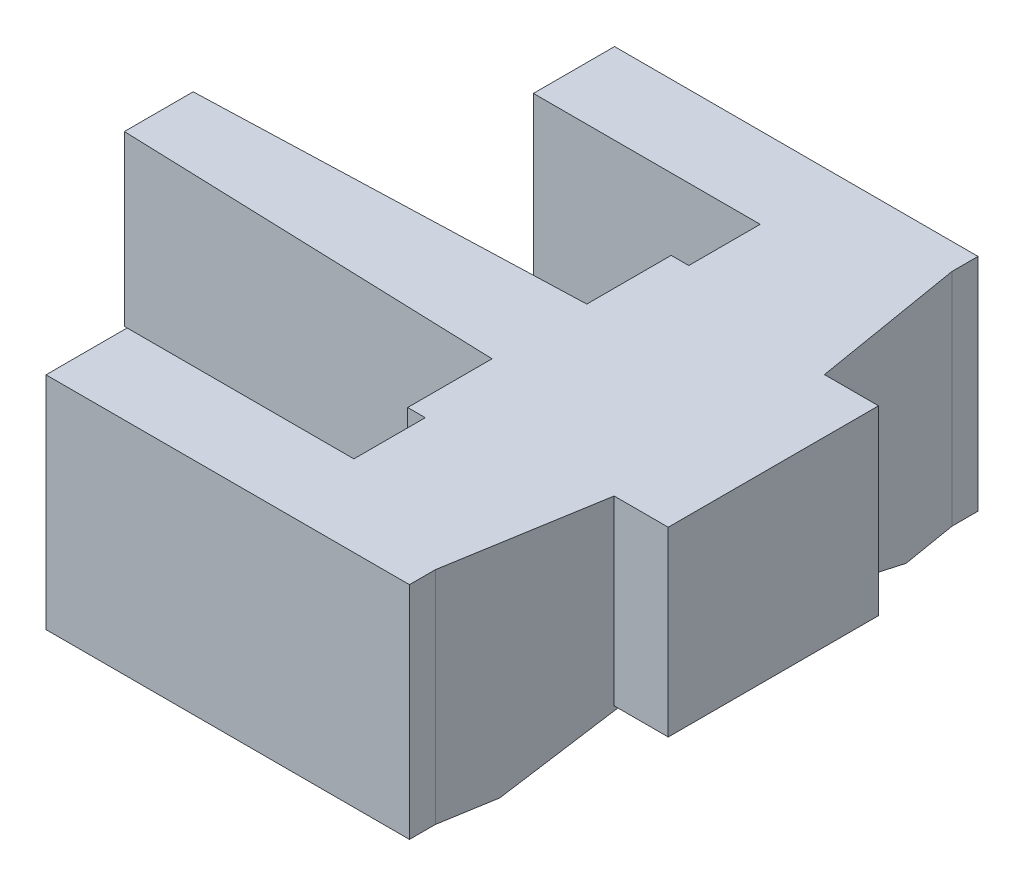
SolidWorks part; units mm, degrees
ref_plane "Front Plane" through (0, 0, 0) normal (0, 0, 1) x (1, 0, 0)
ref_plane "Top Plane" through (0, 0, 0) normal (0, 1, 0) x (1, 0, 0)
ref_plane "Right Plane" through (0, 0, 0) normal (1, 0, 0) x (0, 0, -1)
sketch "Sketch1" plane through (0, 0, 0) normal (0, 1, 0) x (1, 0, 0)
  line L0 (167.303, 457.5748) -> (832.0476, 457.5748) construction
  line L2 (53.2314, 93.5629) -> (55.3687, 80.7629)
  line L3 (55.3687, 80.7629) -> (59.3687, 80.7629)
  line L4 (59.3687, 80.7629) -> (59.3687, 66.5629)
  line L5 (59.3687, 66.5629) -> (55.3687, 66.5629)
  line L6 (55.3687, 66.5629) -> (53.2314, 53.7629)
  line L7 (53.2314, 53.7629) -> (25.2314, 53.7629)
  line L8 (25.2314, 53.7629) -> (25.2314, 58.0129)
  line L9 (25.2314, 58.0129) -> (42.7011, 58.0129)
  line L10 (42.7011, 58.0129) -> (42.7011, 66.5129)
  line L11 (42.7011, 66.5129) -> (41.345, 66.5129)
  line L12 (41.345, 66.5129) -> (41.345, 70.0129)
  line L13 (41.345, 70.0129) -> (12.0187, 71.0129)
  line L14 (12.0187, 71.0129) -> (12.0187, 76.3129)
  line L15 (12.0187, 76.3129) -> (41.345, 77.3129)
  line L16 (41.345, 77.3129) -> (41.345, 80.8129)
  line L17 (41.345, 80.8129) -> (42.7011, 80.8129)
  line L18 (42.7011, 80.8129) -> (42.7011, 89.3129)
  line L19 (42.7011, 89.3129) -> (25.2314, 89.3129)
  line L20 (25.2314, 89.3129) -> (25.2314, 93.5629)
  line L21 (25.2314, 93.5629) -> (53.2314, 93.5629)
  dimension "D1" = 47.35
  dimension "D2" = 39.8
  dimension "D3" = 4.25
  dimension "D4" = 4.25
  dimension "D5" = 12
  dimension "D6" = 12
  dimension "D7" = 3.5
  dimension "D8" = 3.5
  dimension "D9" = 1.3562
  dimension "D10" = 1.3562
  dimension "D11" = 13
  dimension "D12" = 13
  dimension "D13" = 28
  dimension "D14" = 28
  dimension "D15" = 12.8
  dimension "D16" = 12.8
  dimension "D17" = 4
  dimension "D18" = 4
extrude "Boss-Extrude1" add sketch "Sketch1" along normal blind 17
sketch "Sketch2" plane through (0, 0, 0) normal (0, -1, 0) x (1, 0, 0)
  circle A0 centre (42.7011, -73.6629) radius 2.5
extrude "Boss-Extrude2" add sketch "Sketch2" along normal blind 1
sketch "Sketch3" plane through (0, 0, 0) normal (0, -1, 0) x (-1, 0, 0)
  line L0 (-42.7011, 80.8129) -> (-55.3687, 80.7629)
  line L1 (-55.3687, 80.7629) -> (-59.3687, 80.7629)
  line L2 (-59.3687, 80.7629) -> (-59.3687, 66.5629)
  line L3 (-59.3687, 66.5629) -> (-41.345, 66.5129)
  line L4 (-41.345, 66.5129) -> (-41.345, 70.0129)
  line L5 (-41.345, 70.0129) -> (-41.345, 71.5627)
  line L6 (-42.7011, 80.8129) -> (-41.345, 80.8129)
  line L7 (-42.7011, 80.8129) -> (-41.345, 80.8129) construction
  line L8 (-41.345, 80.8129) -> (-41.345, 77.3129) construction
  line L9 (-41.345, 80.8129) -> (-41.345, 77.3129)
  line L10 (-41.345, 77.3129) -> (-41.345, 75.7631)
  circle A0 centre (-42.7011, 73.6629) radius 2.5 construction
  arc A1 (-41.345, 75.7631) -> (-41.345, 71.5627) centre (-42.7011, 73.6629) ccw
extrude "Cut-Extrude1" cut sketch "Sketch3" against normal blind 3
sketch "Sketch4" plane through (0, 0, 0) normal (0, -1, 0) x (1, 0, 0)
  line L0 (41.345, -77.3129) -> (12.0187, -76.3129)
  line L1 (12.0187, -76.3129) -> (12.0187, -71.0129)
  line L2 (12.0187, -71.0129) -> (41.345, -70.0129)
  line L3 (41.345, -70.0129) -> (41.345, -71.5627)
  line L4 (41.345, -77.2209) -> (41.345, -75.7631)
  line L5 (41.345, -75.7631) -> (41.345, -77.3129) construction
  arc A0 (41.345, -71.5627) -> (41.345, -75.7631) centre (42.7011, -73.6629) ccw
extrude "Cut-Extrude5" cut sketch "Sketch4" against normal blind 3 and the other way through all
sketch "Sketch5" plane through (0, 0, -66.5129) normal (0, 0, 1) x (1, 0, 0)
  line L1 (41.345, 3) -> (42.7011, 3)
  line L2 (41.345, 3) -> (41.345, 0)
  line L3 (41.345, 0) -> (42.7011, 0)
  line L4 (42.7011, 3) -> (42.7011, 0)
extrude "Cut-Extrude6" cut sketch "Sketch5" against normal blind 3
sketch "Sketch7" plane through (42.7011, 0, 0) normal (-1, 0, 0) x (0, 0, 1)
  line L0 (-66.5167, 0) -> (-67.2906, 0)
  line L1 (-66.5129, 3) -> (-58.0129, 0)
  line L2 (-58.0129, 0) -> (-66.5167, 0)
  line L3 (-67.2906, 0) -> (-67.2906, 3)
  line L4 (-89.3129, 0) -> (-80.8129, 0)
  line L5 (-67.2906, 3) -> (-66.5129, 3)
  line L6 (-80.8129, 3) -> (-89.3129, 0)
  line L7 (-80.8129, 3) -> (-79.7132, 3)
  line L8 (-79.7132, 3) -> (-79.7132, 0)
  line L9 (-79.7132, 0) -> (-80.8129, 0)
  line L11 (-58.0129, 17) -> (-58.0129, 0) construction
  dimension "D1" = 9.2777
  dimension "D2" = 21.7003
extrude "Cut-Extrude11" cut sketch "Sketch7" against normal blind 20
sketch "Sketch11" plane through (0, 3, 0) normal (0, -1, 0) x (1, 0, 0)
  line L0 (41.345, -77.3129) -> (41.345, -75.7631)
  line L1 (41.345, -77.3129) -> (12.0187, -76.3129)
  line L2 (12.0187, -76.3129) -> (12.0187, -71.0129)
  line L3 (12.0187, -71.0129) -> (41.345, -70.0129)
  line L4 (41.345, -70.0129) -> (41.345, -71.5627)
  arc A0 (41.345, -71.5627) -> (41.345, -75.7631) centre (42.7011, -73.6629) ccw
extrude "Cut-Extrude12" cut sketch "Sketch11" against normal blind 1
sketch "Sketch12" plane through (0, 0, -93.5629) normal (0, 0, -1) x (-1, 0, 0)
  line L1 (-53.2314, 0) -> (-25.2314, 0)
  line L2 (-53.2314, 0) -> (-53.2314, 17)
  line L3 (-53.2314, 17) -> (-25.2314, 17)
  line L4 (-25.2314, 0) -> (-25.2314, 17)
extrude "Boss-Extrude3" add sketch "Sketch12" along normal blind 2
sketch "Sketch13" plane through (0, 0, -53.7629) normal (0, 0, 1) x (1, 0, 0)
  line L1 (53.2314, 17) -> (25.2314, 17)
  line L2 (53.2314, 17) -> (53.2314, 0)
  line L3 (53.2314, 0) -> (25.2314, 0)
  line L4 (25.2314, 17) -> (25.2314, 0)
extrude "Boss-Extrude4" add sketch "Sketch13" along normal blind 2
sketch "Sketch14" plane through (0, 0, -66.5129) normal (0, 0, 1) x (1, 0, 0)
  line L1 (42.7011, 17) -> (41.345, 17)
  line L2 (42.7011, 17) -> (42.7011, 3)
  line L3 (42.7011, 3) -> (41.345, 3)
  line L4 (41.345, 17) -> (41.345, 3)
extrude "Boss-Extrude5" add sketch "Sketch14" along normal blind 1
sketch "Sketch15" plane through (0, 0, -80.8129) normal (0, 0, -1) x (-1, 0, 0)
  line L1 (-42.7011, 17) -> (-41.345, 17)
  line L2 (-42.7011, 17) -> (-42.7011, 3)
  line L3 (-42.7011, 3) -> (-41.345, 3)
  line L4 (-41.345, 17) -> (-41.345, 3)
extrude "Boss-Extrude6" add sketch "Sketch15" along normal blind 1
sketch "Sketch16" plane through (0, 0, -66.5629) normal (0, 0, 1) x (1, 0, 0)
  line L0 (59.3687, 17) -> (59.3687, 3) construction
  line L1 (59.3687, 3) -> (55.3687, 3)
  line L2 (59.3687, 3) -> (59.3687, 17)
  line L3 (59.3687, 17) -> (55.3687, 17)
  line L5 (55.3687, 17) -> (53.6672, 17)
  line L7 (55.3687, 3) -> (53.6672, 3)
  line L8 (53.6672, 17) -> (53.6672, 3)
  dimension "D1" = 5.7015
extrude "Boss-Extrude7" add sketch "Sketch16" along normal blind 1
sketch "Sketch17" plane through (0, 0, -80.7629) normal (0, 0, -1) x (-1, 0, 0)
  line L0 (-55.3687, 17) -> (-55.3687, 3) construction
  line L1 (-59.3687, 3) -> (-55.3687, 3)
  line L2 (-59.3687, 3) -> (-59.3687, 17)
  line L3 (-59.3687, 17) -> (-55.3687, 17)
  line L5 (-55.3687, 17) -> (-53.078, 17)
  line L7 (-55.3687, 3) -> (-53.078, 3)
  line L8 (-53.078, 17) -> (-53.078, 3)
  dimension "D1" = 2.2906
extrude "Boss-Extrude8" add sketch "Sketch17" along normal blind 1
sketch "Sketch18" plane through (0, 0, -65.5129) normal (0, 0, 1) x (1, 0, 0)
  line L1 (42.7011, 17) -> (41.345, 17)
  line L2 (42.7011, 17) -> (42.7011, 3)
  line L3 (42.7011, 3) -> (41.345, 3)
  line L4 (41.345, 17) -> (41.345, 3)
extrude "Boss-Extrude9" add sketch "Sketch18" along normal blind 2
sketch "Sketch19" plane through (0, 0, -81.8129) normal (0, 0, -1) x (-1, 0, 0)
  line L1 (-42.7011, 3) -> (-41.345, 3)
  line L2 (-42.7011, 3) -> (-42.7011, 17)
  line L3 (-42.7011, 17) -> (-41.345, 17)
  line L4 (-41.345, 3) -> (-41.345, 17)
extrude "Boss-Extrude10" add sketch "Sketch19" along normal blind 2
